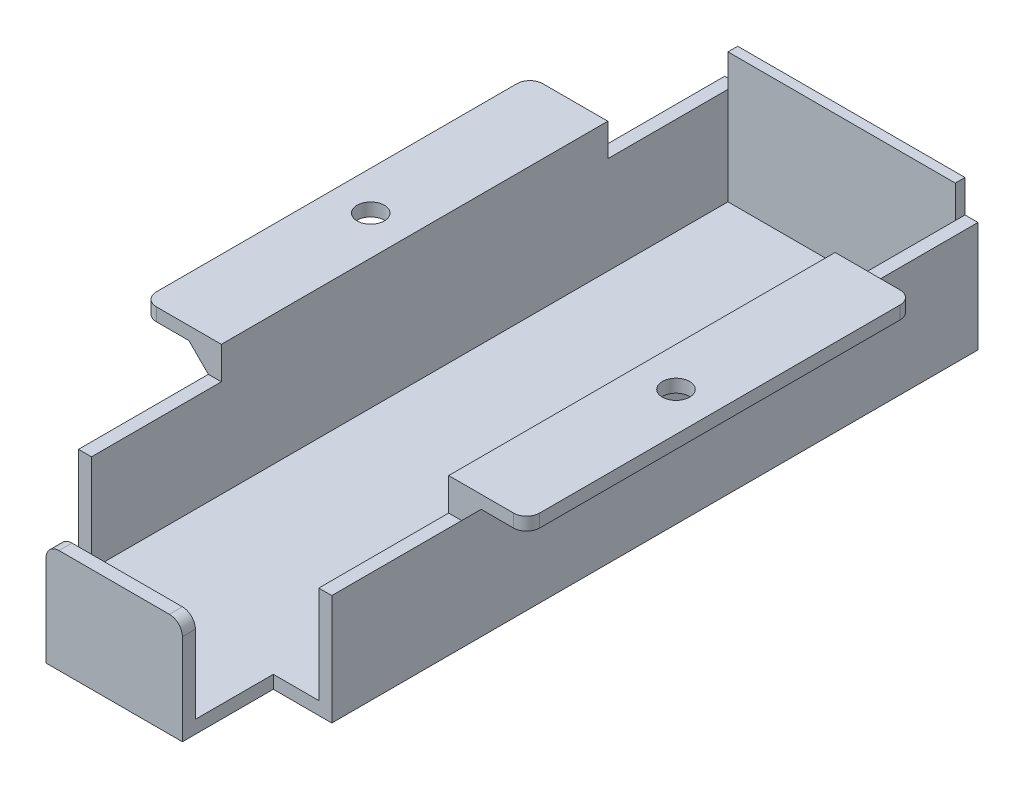
SolidWorks part; units mm, degrees
ref_plane "Front Plane" through (0, 0, 0) normal (0, 0, 1) x (1, 0, 0)
ref_plane "Top Plane" through (0, 0, 0) normal (0, 1, 0) x (1, 0, 0)
ref_plane "Right Plane" through (0, 0, 0) normal (1, 0, 0) x (0, 0, -1)
sketch "Sketch1" plane through (0, 0, 0) normal (0, 0, 1) x (1, 0, 0)
  line L0 (-29.5, 0) -> (-17.5, 0)
  line L1 (-17.5, 0) -> (-17.5, -20)
  line L2 (-17.5, -20) -> (17.5, -20)
  line L3 (0, -618.9467) -> (0, 30328.3864) construction
  line L5 (29.5, -2) -> (29.5, 0)
  line L6 (19.5, -2) -> (29.5, -2)
  line L7 (19.5, -22) -> (19.5, -2)
  line L8 (19.5, -22) -> (-19.5, -22)
  line L9 (-19.5, -22) -> (-19.5, -2)
  line L10 (-19.5, -2) -> (-29.5, -2)
  line L11 (-29.5, -2) -> (-29.5, 0)
  line L12 (17.5, 0) -> (17.5, -20)
  line L13 (29.5, 0) -> (17.5, 0)
  dimension "D1" = 35
  dimension "D2" = 20
  dimension "D3" = 2
  dimension "D4" = 2
  dimension "D5" = 2
  dimension "D6" = 10
extrude "Boss-Extrude1" add sketch "Sketch1" along normal mid plane 98
sketch "Sketch3" plane through (0, 0, 0) normal (1, 0, 0) x (0, 0, -1)
  line L0 (-49, -22) -> (-63, -22)
  line L1 (-63, -22) -> (-63, -6)
  line L2 (-63, -6) -> (-61, -6)
  line L3 (-61, -6) -> (-61, -20)
  line L4 (-61, -20) -> (-49, -20)
  line L5 (-49, -22) -> (-49, -2) construction
  line L6 (-49, -20) -> (-49, -22)
  line L8 (49, -20) -> (49, 0) construction
  dimension "D3" = 2
  dimension "D2" = 2
  dimension "D4" = 16
  dimension "D1" = 110
extrude "Boss-Extrude3" add sketch "Sketch3" along normal mid plane 21
chamfer "Chamfer1" distance 3 angle 45 2 edges at (19.5, -2, 0) (-19.5, -2, 0)
sketch "Sketch4" plane through (0, 0, 0) normal (0, 1, 0) x (1, 0, 0)
  line L0 (-23.5, 0) -> (23.5, 0) construction
  circle A0 centre (-23.5, 0) radius 2.1
  circle A1 centre (23.5, 0) radius 2.1
  point P4 (0, 0)
  dimension "D1" = 4.2
  dimension "D2" = 4.2
  dimension "D3" = 47
extrude "Cut-Extrude1" cut sketch "Sketch4" against normal through all
sketch "Sketch5" plane through (0, -2, 0) normal (0, -1, 0) x (1, 0, 0)
  line L0 (19.5, -49) -> (19.5, 49) construction
  line L1 (27.5, -5) -> (19.5, -5)
  line L2 (27.5, -5) -> (27.5, 5)
  line L3 (27.5, 5) -> (19.5, 5)
  line L4 (19.5, -5) -> (19.5, 5)
  line L5 (27.5, -5) -> (19.5, 5) construction
  line L6 (27.5, 5) -> (19.5, -5) construction
  line L7 (-19.5, 49) -> (-19.5, -49) construction
  line L8 (-27.5, -5) -> (-19.5, -5)
  line L9 (-27.5, -5) -> (-27.5, 5)
  line L10 (-27.5, 5) -> (-19.5, 5)
  line L11 (-19.5, -5) -> (-19.5, 5)
  line L12 (-27.5, -5) -> (-19.5, 5) construction
  line L13 (-27.5, 5) -> (-19.5, -5) construction
  point P0 (23.5, 0)
  point P8 (-23.5, 0)
  dimension "D1" = 10
extrude "Cut-Extrude2" cut sketch "Sketch5" along normal through all
sketch "Sketch2" plane through (0, 0, -49) normal (0, 0, -1) x (-1, 0, 0)
  line L0 (-17.5, 0) -> (17.5, 0)
  line L18 (29.5, -2) -> (29.5, 0)
  line L19 (29.5, 0) -> (17.5, 0)
  line L20 (17.5, 0) -> (17.5, -20)
  line L21 (17.5, -20) -> (-17.5, -20)
  line L22 (-17.5, -20) -> (-17.5, 0)
  line L23 (-17.5, 0) -> (-29.5, 0)
  line L24 (-29.5, 0) -> (-29.5, -2)
  line L25 (-29.5, -2) -> (-22.5, -2)
  line L26 (-22.5, -2) -> (-19.5, -5)
  line L27 (-19.5, -5) -> (-19.5, -22)
  line L28 (-19.5, -22) -> (19.5, -22)
  line L29 (19.5, -22) -> (19.5, -5)
  line L30 (19.5, -5) -> (22.5, -2)
  line L31 (22.5, -2) -> (29.5, -2)
  line L32 (29.5, -2) -> (29.5, 0)
  line L33 (29.5, 0) -> (17.5, 0)
  line L37 (-17.5, 0) -> (-29.5, 0)
  line L38 (-29.5, 0) -> (-29.5, -2)
  line L39 (-29.5, -2) -> (-22.5, -2)
  line L40 (-22.5, -2) -> (-19.5, -5)
  line L41 (-19.5, -5) -> (-19.5, -22)
  line L42 (-19.5, -22) -> (19.5, -22)
  line L43 (19.5, -22) -> (19.5, -5)
  line L44 (19.5, -5) -> (22.5, -2)
  line L45 (22.5, -2) -> (29.5, -2)
  dimension "D1" = 0
extrude "Boss-Extrude5" add sketch "Sketch2" along normal blind 1.5
sketch "Sketch6" plane through (0, 0, 0) normal (0, 1, 0) x (1, 0, 0)
  line L0 (-17.5, -49) -> (-17.5, 49) construction
  line L1 (-29.5, -49) -> (-17.5, -49)
  line L2 (-29.5, -49) -> (-29.5, -29)
  line L3 (-29.5, -29) -> (-17.5, -29)
  line L4 (-17.5, -49) -> (-17.5, -29)
  line L5 (17.5, -49) -> (17.5, 49) construction
  line L6 (29.5, -49) -> (17.5, -49)
  line L7 (29.5, -49) -> (29.5, -29)
  line L8 (29.5, -29) -> (17.5, -29)
  line L9 (17.5, -49) -> (17.5, -29)
  line L11 (29.5, 50.5) -> (17.5, 50.5)
  line L12 (29.5, 50.5) -> (29.5, 30.5)
  line L13 (29.5, 30.5) -> (17.5, 30.5)
  line L14 (17.5, 50.5) -> (17.5, 30.5)
  line L15 (-29.5, 50.5) -> (-17.5, 50.5)
  line L16 (-29.5, 50.5) -> (-29.5, 30.5)
  line L17 (-29.5, 30.5) -> (-17.5, 30.5)
  line L18 (-17.5, 50.5) -> (-17.5, 30.5)
  dimension "D1" = 20
extrude "Cut-Extrude3" cut sketch "Sketch6" against normal up to vertex (5 mm away)
fillet "Fillet1" radius 2 6 edges at (-29.5, -1, 29) (-29.5, -1, -30.5) (29.5, -1, -30.5) (29.5, -1, 29) (-10.5, -6, 62) (10.5, -6, 62)
equation "\"D4@Sketch1\"=\"D3@Sketch1\""
equation "\"D5@Sketch1\"=\"D3@Sketch1\""
equation "\"D2@Sketch3\"=\"D3@Sketch3\""
equation "\"width\"= 24"
equation "\"thk\"= 3"
equation "\"holesize\"= 4.2"
equation "\"holedistance\"= ( 20 + 12 ) / 2"
equation "\"threaded_hole\"= 3.9"
equation "\"fillet_radius\"= 2"
equation "\"ground_clearance\"= 25"
equation "\"tire_thk\"= 3"
equation "\"innerwheel_diam\" = \"wheel_diam\"-2*\"tire_thk\""
equation "\"innerwheel_thk\"= 8"
equation "\"wheel_diam\"= 2*(\"width\"/2+\"ground_clearance\")"
equation "\"coloursensor_holesize\"= 2.65"
equation "\"hole_to_edge\" = 4"
equation "\"D1@Sketch4\"=\"holesize\""
equation "\"D2@Sketch4\"=\"D1@Sketch4\""
